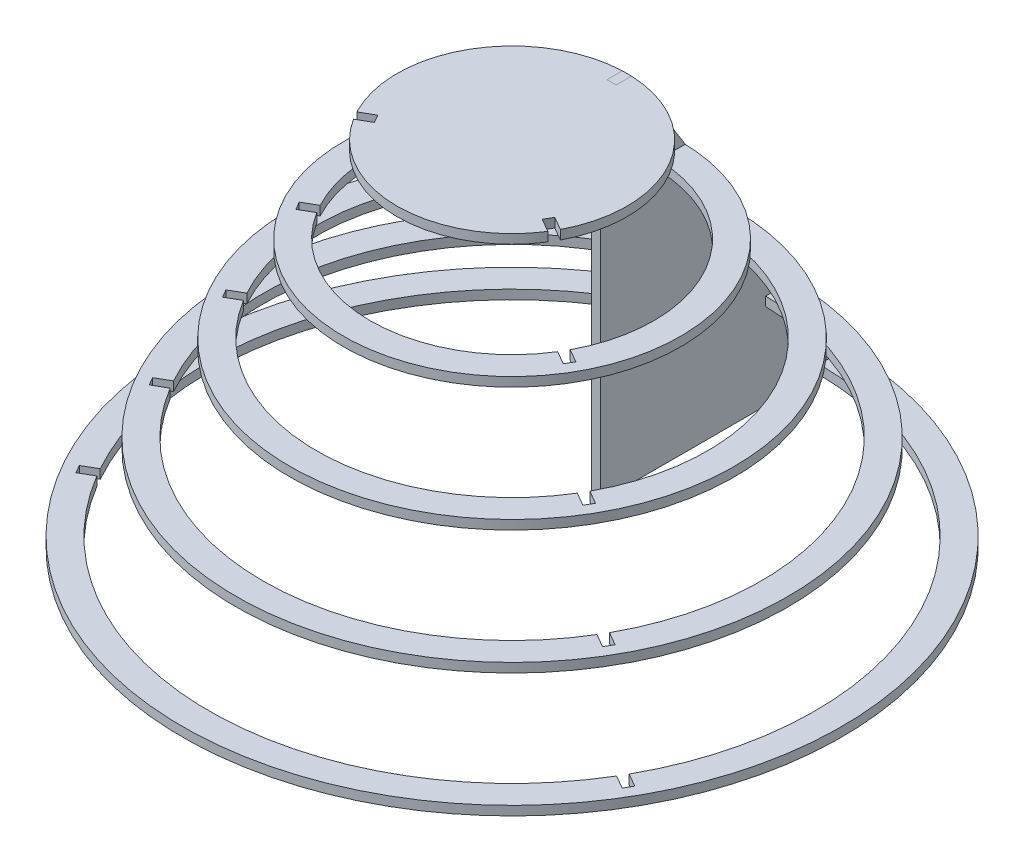
SolidWorks part; units mm, degrees
ref_plane "Front Plane" through (0, 0, 0) normal (0, 0, 1) x (1, 0, 0)
ref_plane "Top Plane" through (0, 0, 0) normal (0, 1, 0) x (1, 0, 0)
ref_plane "Right Plane" through (0, 0, 0) normal (1, 0, 0) x (0, 0, -1)
sketch "Sketch1" plane through (0, 0, 0) normal (0, 1, 0) x (1, 0, 0)
  line L0 (109.4793, -70.1361) -> (126.7998, -80.1361)
  line L1 (6, 129.88) -> (6, 149.88)
  line L2 (-6, 129.88) -> (-6, 149.88)
  line L3 (115.4793, -59.7438) -> (132.7998, -69.7438)
  line L4 (-6, 129.88) -> (6, 129.88)
  line L5 (115.4793, -59.7438) -> (109.4793, -70.1361)
  line L6 (-115.4793, -59.7438) -> (-132.7998, -69.7438)
  line L7 (-109.4793, -70.1361) -> (-126.7998, -80.1361)
  line L8 (-109.4793, -70.1361) -> (-115.4793, -59.7438)
  arc A0 (-6, 149.88) -> (-132.7998, -69.7438) centre (0, 0) ccw
  arc A1 (-126.7998, -80.1361) -> (126.7998, -80.1361) centre (0, 0) ccw
  arc A2 (132.7998, -69.7438) -> (6, 149.88) centre (0, 0) ccw
  point P17 (0, 0)
  dimension "D1" = 300
  dimension "D2" = 3
extrude "Boss-Extrude1" add sketch "Sketch1" along normal blind 12
ref_plane "Plane1" through (0, -100, 0) normal (0, -1, 0) x (-1, 0, 0)
sketch "Sketch2" plane through (0, -100, 0) normal (0, -1, 0) x (-1, 0, 0)
  line L0 (180.4368, -97.2471) -> (163.1304, -87.2552)
  line L1 (-6, 204.8864) -> (-6, 184.9027)
  line L2 (6, 204.8864) -> (6, 184.9027)
  line L3 (6, 204.8864) -> (-6, 204.8864)
  line L4 (174.4368, -107.6394) -> (157.1304, -97.6475)
  line L5 (174.4368, -107.6394) -> (180.4368, -97.2471)
  line L6 (-174.4368, -107.6394) -> (-157.1304, -97.6475)
  line L7 (-180.4368, -97.2471) -> (-163.1304, -87.2552)
  line L8 (-180.4368, -97.2471) -> (-174.4368, -107.6394)
  circle A0 centre (0, 0) radius 220
  arc A1 (-6, 184.9027) -> (-163.1304, -87.2552) centre (0, 0) ccw
  circle A2 centre (0, 0) radius 185 construction
  arc A3 (163.1304, -87.2552) -> (6, 184.9027) centre (0, 0) ccw
  arc A4 (-157.1304, -97.6475) -> (157.1304, -97.6475) centre (0, 0) ccw
  point P22 (0, 0)
  dimension "D1" = 35
  dimension "D2" = 370
  dimension "D3" = 3
extrude "Boss-Extrude2" add sketch "Sketch2" along normal blind 12 separate body
ref_plane "Plane2" through (0, -212, 0) normal (0, -1, 0) x (-1, 0, 0)
sketch "Sketch3" plane through (0, -212, 0) normal (0, -1, 0) x (-1, 0, 0)
  line L0 (241.0958, -132.2685) -> (223.7753, -122.2685)
  line L1 (235.0958, -142.6609) -> (217.7753, -132.6609)
  line L2 (-6, 274.9294) -> (-6, 254.9294)
  line L3 (6, 274.9294) -> (6, 254.9294)
  line L4 (6, 274.9294) -> (-6, 274.9294)
  line L5 (235.0958, -142.6609) -> (241.0958, -132.2685)
  line L6 (-235.0958, -142.6609) -> (-217.7753, -132.6609)
  line L7 (-241.0958, -132.2685) -> (-223.7753, -122.2685)
  line L8 (-241.0958, -132.2685) -> (-235.0958, -142.6609)
  arc A0 (-6, 254.9294) -> (-223.7753, -122.2685) centre (0, 0) ccw
  circle A1 centre (0, 0) radius 290
  circle A2 centre (0, 0) radius 255 construction
  arc A3 (223.7753, -122.2685) -> (6, 254.9294) centre (0, 0) ccw
  arc A4 (-217.7753, -132.6609) -> (217.7753, -132.6609) centre (0, 0) ccw
  point P19 (0, 0)
  dimension "D1" = 35
  dimension "D2" = 510
  dimension "D3" = 3
extrude "Boss-Extrude3" add sketch "Sketch3" along normal blind 12 separate body
ref_plane "Plane3" through (0, -324, 0) normal (0, -1, 0) x (-1, 0, 0)
sketch "Sketch4" plane through (0, -324, 0) normal (0, -1, 0) x (-1, 0, 0)
  line L0 (301.7308, -167.2762) -> (284.4103, -157.2762)
  line L1 (295.7308, -177.6685) -> (278.4103, -167.6685)
  line L2 (-6, 344.9446) -> (-6, 324.9446)
  line L3 (6, 344.9446) -> (6, 324.9446)
  line L4 (6, 344.9446) -> (-6, 344.9446)
  line L5 (295.7308, -177.6685) -> (301.7308, -167.2762)
  line L6 (-295.7308, -177.6685) -> (-278.4103, -167.6685)
  line L7 (-301.7308, -167.2762) -> (-284.4103, -157.2762)
  line L8 (-301.7308, -167.2762) -> (-295.7308, -177.6685)
  arc A0 (-6, 324.9446) -> (-284.4103, -157.2762) centre (0, 0) ccw
  circle A1 centre (0, 0) radius 360
  circle A2 centre (0, 0) radius 325 construction
  arc A3 (284.4103, -157.2762) -> (6, 324.9446) centre (0, 0) ccw
  arc A4 (-278.4103, -167.6685) -> (278.4103, -167.6685) centre (0, 0) ccw
  point P19 (0, 0)
  dimension "D1" = 650
  dimension "D3" = 3
  dimension "D2" = 35
extrude "Boss-Extrude4" add sketch "Sketch4" along normal blind 12 separate body
ref_plane "Plane4" through (0, -436, 0) normal (0, -1, 0) x (-1, 0, 0)
sketch "Sketch5" plane through (0, -436, 0) normal (0, -1, 0) x (-1, 0, 0)
  line L0 (362.3611, -202.2811) -> (345.0406, -192.2811)
  line L1 (356.3611, -212.6734) -> (339.0406, -202.6734)
  line L2 (-6, 414.9544) -> (-6, 394.9544)
  line L3 (6, 414.9544) -> (6, 394.9544)
  line L4 (6, 414.9544) -> (-6, 414.9544)
  line L5 (356.3611, -212.6734) -> (362.3611, -202.2811)
  line L6 (-356.3611, -212.6734) -> (-339.0406, -202.6734)
  line L7 (-362.3611, -202.2811) -> (-345.0406, -192.2811)
  line L8 (-362.3611, -202.2811) -> (-356.3611, -212.6734)
  arc A0 (-6, 394.9544) -> (-345.0406, -192.2811) centre (0, 0) ccw
  circle A1 centre (0, 0) radius 430
  circle A2 centre (0, 0) radius 395 construction
  arc A3 (345.0406, -192.2811) -> (6, 394.9544) centre (0, 0) ccw
  arc A4 (-339.0406, -202.6734) -> (339.0406, -202.6734) centre (0, 0) ccw
  point P19 (0, 0)
  dimension "D1" = 35
  dimension "D2" = 790
  dimension "D3" = 3
extrude "Boss-Extrude5" add sketch "Sketch5" along normal blind 12 separate body
sketch "Sketch7" plane through (-6, 0, 0) normal (1, 0, 0) x (0, 0, -1)
  line L3 (109.6881, -448) -> (414.9544, -448)
  line L4 (414.9544, -448) -> (414.9544, -436)
  line L5 (414.9544, -436) -> (430, -436)
  line L6 (360, -336) -> (344.9446, -336)
  line L7 (344.9446, -336) -> (344.9446, -324)
  line L8 (344.9446, -324) -> (360, -324)
  line L9 (360, -324) -> (290, -224)
  line L10 (290, -224) -> (274.9294, -224)
  line L11 (274.9294, -224) -> (274.9294, -212)
  line L12 (274.9294, -212) -> (290, -212)
  line L13 (290, -212) -> (220, -112)
  line L14 (220, -112) -> (220, -100) construction
  line L15 (220, -112) -> (204.8864, -112)
  line L16 (204.8864, -112) -> (204.8864, -100)
  line L17 (204.8864, -100) -> (220, -100)
  line L18 (220, -100) -> (149.88, 12)
  line L19 (149.88, 12) -> (129.88, 12)
  line L20 (129.88, 12) -> (129.88, 0)
  line L21 (129.88, 0) -> (109.6881, 0)
  line L22 (430, -436) -> (360, -336)
  line L23 (109.6881, 0) -> (109.6881, -448)
extrude "Boss-Extrude6" add sketch "Sketch7" along normal blind 12 separate body
